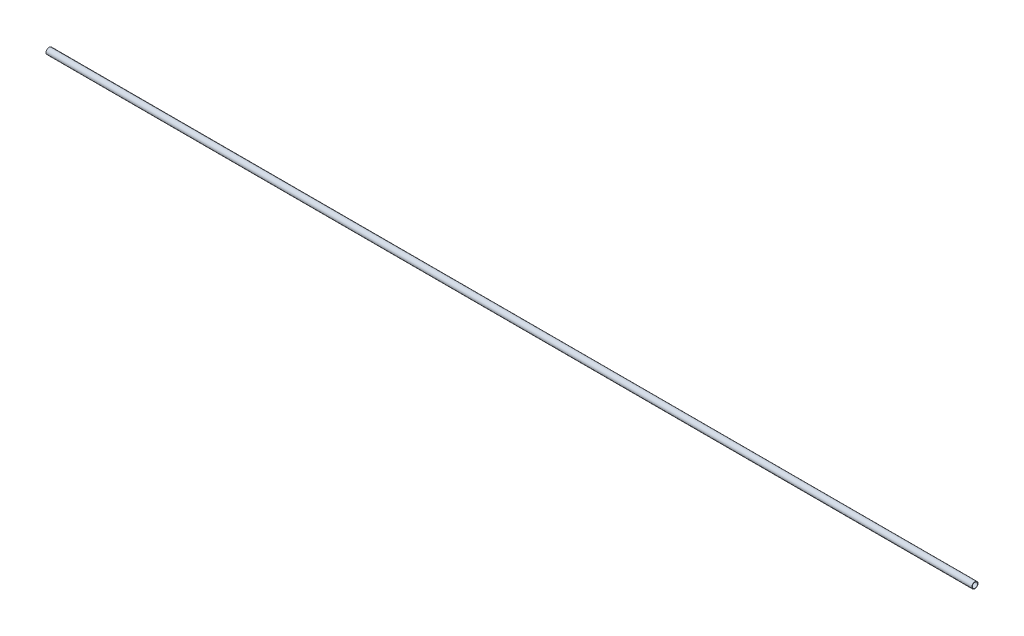
SolidWorks part; units mm, degrees
material "6061-T6 (SS)"
ref_plane "Front Plane" through (0, 0, 0) normal (0, 0, 1) x (1, 0, 0)
ref_plane "Top Plane" through (0, 0, 0) normal (0, 1, 0) x (1, 0, 0)
ref_plane "Right Plane" through (0, 0, 0) normal (1, 0, 0) x (0, 0, -1)
sketch "Sketch1" plane through (0, 0, 0) normal (0, 1, 0) x (1, 0, 0)
  line L0 (0, 0) -> (711.2, 0)
  line L3 (0, 0) -> (0, 37.5) construction
  dimension "D1" = 711.2
sketch "Sketch2" plane through (0, 0, 0) normal (1, 0, 0) x (0, 0, -1)
  circle A0 centre (0, 0) radius 2.3813
  circle A1 centre (0, 0) radius 2.0256
  dimension "D1" = 4.7625
  dimension "D2" = 0.3556
sweep "Sweep1" add profiles "Sketch2" path "Sketch1"
